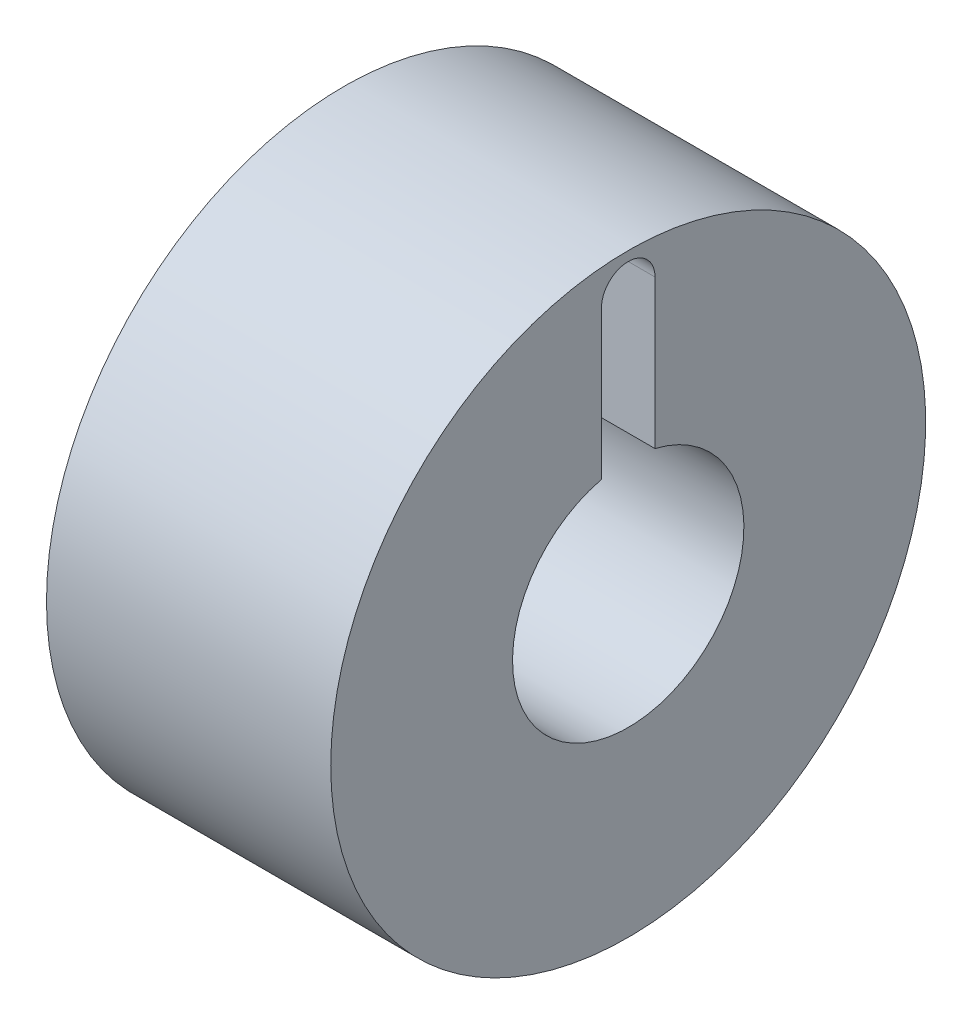
SolidWorks part; units mm, degrees
material "AISI 316 Annealed Stainless Steel Bar (SS)"
ref_plane "Front Plane" through (0, 0, 0) normal (0, 0, 1) x (1, 0, 0)
ref_plane "Top Plane" through (0, 0, 0) normal (0, 1, 0) x (1, 0, 0)
ref_plane "Right Plane" through (0, 0, 0) normal (1, 0, 0) x (0, 0, -1)
sketch "Sketch3" plane through (0, 0, 0) normal (0, 0, 1) x (1, 0, 0)
  line L0 (-58.5481, 189.9573) -> (284.033, 189.9573) construction
  line L2 (213.4012, -189.6279) -> (558.7345, -189.6279) construction
  line L4 (227.3705, -148.5737) -> (308.4812, -148.5737) construction
  line L33 (253.3852, -145.0737) -> (253.3852, -140.8737)
  line L38 (250.6852, -139.5737) -> (259.2852, -139.5737)
  line L87 (250.6852, -140.8737) -> (253.3852, -140.8737)
  line L93 (259.2852, -139.5737) -> (259.2852, -140.8572)
  line L95 (250.6852, -139.5737) -> (250.6852, -140.8737)
  line L96 (253.3852, -145.0737) -> (259.2852, -145.0737)
  line L97 (259.2852, -145.0737) -> (259.2852, -140.8572)
  line L112 (261.9184, -141.0941) -> (261.9184, -140.8247)
  dimension "D1" = 9
  dimension "D2" = 8.6
  dimension "D3" = 7.7
  dimension "D4" = 2.7
  dimension "D6" = 3.5
revolve "Revolve1" add sketch "Sketch3" angle 360 about L4
sketch3d "3DSketch1"
  line L0 (259.2852, -148.5737, 0) -> (253.3852, -148.5737, 0) construction
  line L1 (253.3852, -148.5737, 0) -> (253.3852, -140.6737, 0) construction
  line L2 (259.2852, -148.5737, 0) -> (259.2852, -144.4737, 0) construction
  line L3 (259.2852, -144.4737, 0) -> (253.3852, -140.6737, 0)
  circle A0 centre (259.2852, -148.5737, 0) radius 4.1 construction
  circle A2 centre (253.3852, -148.5737, 0) radius 7.9 construction
  point P2 (263.3852, -148.5737, 0)
  point P7 (245.4852, -148.5737, 0)
sketch "Sketch11" plane through (259.2852, 0, 0) normal (1, 0, 0) x (0, 0, -1)
  line L0 (-0.81, -140.6737) -> (-0.81, -145.1687)
  line L1 (0.81, -140.6737) -> (0.81, -145.1687)
  line L2 (0.81, -145.1687) -> (-0.81, -145.1687)
  arc A1 (0.81, -140.6737) -> (-0.81, -140.6737) centre (0, -140.6737) ccw
  circle A2 centre (0, -148.5737) radius 3.5 construction
  point P0 (0.81, -145.1687)
extrude "Cut-Extrude1" cut sketch "Sketch11" against normal up to next
